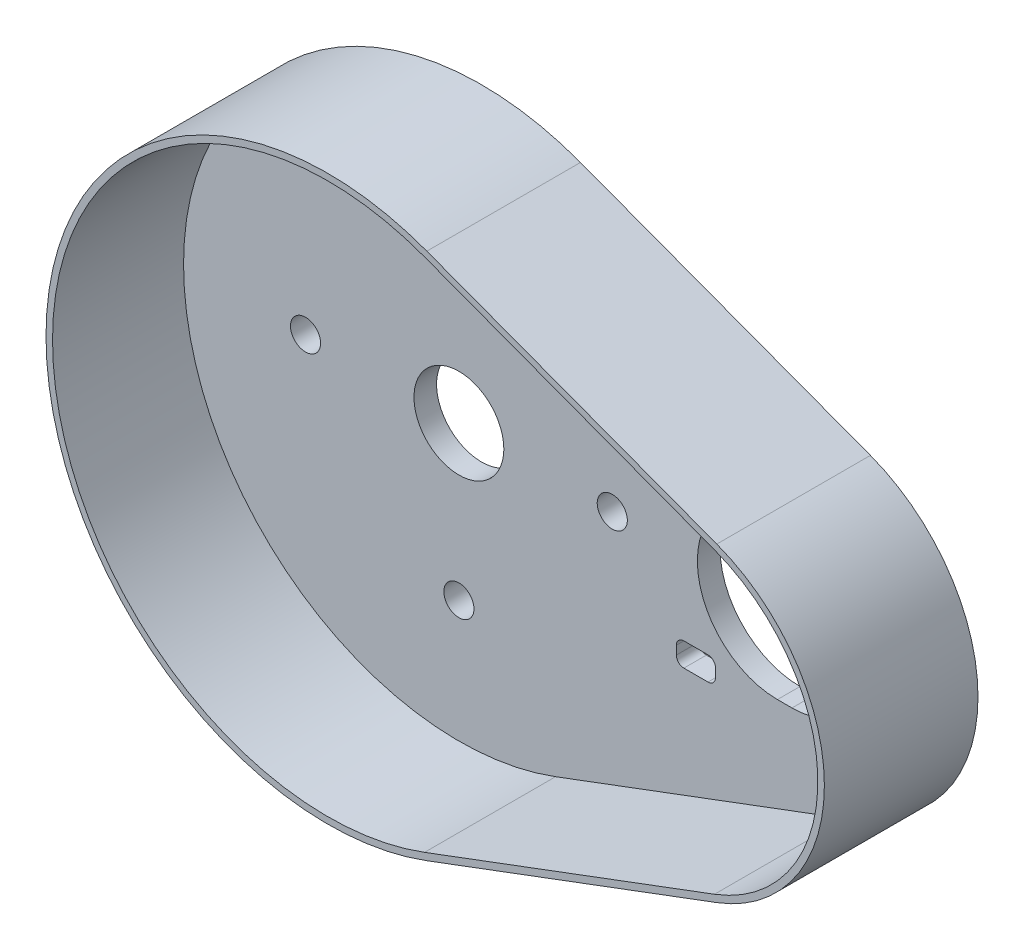
SolidWorks part; units mm, degrees
ref_plane "Front Plane" through (0, 0, 0) normal (0, 0, 1) x (1, 0, 0)
ref_plane "Top Plane" through (0, 0, 0) normal (0, 1, 0) x (1, 0, 0)
ref_plane "Right Plane" through (0, 0, 0) normal (1, 0, 0) x (0, 0, -1)
sketch "Sketch1" plane through (0, 0, 0) normal (0, 0, 1) x (1, 0, 0)
  line L0 (-8.95, 0) -> (-56.15, 0) construction
  line L1 (-8.95, 0) -> (33.55, 0) construction
  line L2 (63.45, 0) -> (66.35, 0) construction
  line L3 (63.45, 15.95) -> (66.35, 15.95)
  line L4 (63.45, -15.95) -> (66.35, -15.95)
  line L5 (78.3116, -15.15) -> (86.1116, -15.15)
  line L18 (19.7099, 52.577) -> (77.466, 30.9257)
  line L19 (19.7099, -52.577) -> (77.466, -30.9257)
  line L20 (47.5, 0) -> (82.3, 0) construction
  line L21 (98.9, 0) -> (98.9, 11.6645) construction
  line L22 (85.6834, -19.3995) -> (89.4701, -23.1076) construction
  line L23 (85.6834, -19.3995) -> (82.3815, -22.7713) construction
  line L24 (90.4593, -22.0975) -> (89.4701, -23.1076) construction
  line L25 (53.255, -12.2664) -> (52.7151, -11.8177) construction
  line L26 (53.255, -12.2664) -> (50.5704, -15.4964) construction
  line L27 (50.5704, -15.4964) -> (55.3829, -19.4962) construction
  line L28 (43.3116, 19.85) -> (51.1116, 19.85)
  line L29 (43.3116, 19.85) -> (43.3116, 15.15)
  line L30 (43.3116, 15.15) -> (51.1116, 15.15)
  line L31 (51.1116, 19.85) -> (51.1116, 15.15)
  line L32 (78.3116, 19.85) -> (86.1116, 19.85)
  line L33 (78.3116, 19.85) -> (78.3116, 15.15)
  line L34 (78.3116, 15.15) -> (86.1116, 15.15)
  line L35 (86.1116, 19.85) -> (86.1116, 15.15)
  line L36 (86.1116, -19.85) -> (86.1116, -15.15)
  line L37 (78.3116, -19.85) -> (86.1116, -19.85)
  line L38 (78.3116, -19.85) -> (78.3116, -15.15)
  line L39 (43.3116, -15.15) -> (51.1116, -15.15)
  line L40 (51.1116, -19.85) -> (51.1116, -15.15)
  line L41 (43.3116, -19.85) -> (51.1116, -19.85)
  line L42 (43.3116, -19.85) -> (43.3116, -15.15)
  circle A0 centre (0, 0) radius 56.15
  circle A1 centre (0, 0) radius 8.95
  circle A2 centre (0, 0) radius 30.55 construction
  circle A3 centre (0, 30.55) radius 3
  circle A4 centre (30.55, 0) radius 3
  circle A5 centre (0, -30.55) radius 3
  circle A6 centre (-30.55, 0) radius 3
  circle A7 centre (65.8727, 0) radius 33.0273
  arc A8 (63.45, 15.95) -> (63.45, -15.95) centre (63.45, 0) ccw
  arc A9 (66.35, -15.95) -> (66.35, 15.95) centre (66.35, 0) ccw
  circle A18 centre (84.6116, -18.35) radius 1.5 construction
  circle A19 centre (49.6116, -16.65) radius 1.5 construction
  point P18 (64.9, 0)
  point P45 (54.7266, -18.4736)
  point P46 (52.6747, -14.817)
  point P47 (52.4978, -14.8563)
  point P48 (52.6941, -15.0718)
  point P49 (86.8305, -19.3443)
  point P50 (43.3116, -17.5)
  point P62 (8.95, 0)
  dimension "D1" = 17.9
  dimension "D2" = 6
  dimension "D5" = 7.8
  dimension "D9" = 31.9
  dimension "D12" = 16.6
  dimension "D7" = 3
  dimension "D3" = 47.2
  dimension "D4" = 42.5
  dimension "D6" = 4.7
  dimension "D8" = 42.8
  dimension "D10" = 34.8
  dimension "D11" = 38.55
  dimension "D13" = 155.05
  dimension "D14" = 5.3
  dimension "D15" = 39.7
  dimension "D16" = 4.2
extrude "Boss-Extrude1" add sketch "Sketch1" along normal blind 30.6
sketch "Sketch2" plane through (0, 0, 30.6) normal (0, 0, 1) x (1, 0, 0)
  line L6 (77.0097, 29.7084) -> (19.2535, 51.3598)
  line L7 (19.2535, -51.3598) -> (77.0097, -29.7084)
  line L8 (77.0097, 29.7084) -> (19.2535, 51.3598)
  line L9 (19.2535, -51.3598) -> (77.0097, -29.7084)
  arc A8 (19.2535, 51.3598) -> (19.2535, -51.3598) centre (0, 0) ccw
  arc A9 (77.0097, -29.7084) -> (77.0097, 29.7084) centre (65.8727, 0) ccw
  arc A10 (19.2535, 51.3598) -> (19.2535, -51.3598) centre (0, 0) ccw
  arc A11 (77.0097, -29.7084) -> (77.0097, 29.7084) centre (65.8727, 0) ccw
  dimension "D1" = 1.3
extrude "Cut-Extrude1" cut sketch "Sketch2" against normal blind 26.1
fillet "Filete1" radius 1.5 16 edges at (78.3116, 15.15, 2.25) (78.3116, 19.85, 2.25) (86.1116, 19.85, 2.25) (86.1116, 15.15, 2.25) (51.1116, 15.15, 2.25) (51.1116, 19.85, 2.25) (43.3116, 19.85, 2.25) (43.3116, 15.15, 2.25) (43.3116, -19.85, 2.25) (51.1116, -19.85, 2.25) (51.1116, -15.15, 2.25) (43.3116, -15.15, 2.25) (78.3116, -15.15, 2.25) (78.3116, -19.85, 2.25) (86.1116, -15.15, 2.25) (86.1116, -19.85, 2.25)
